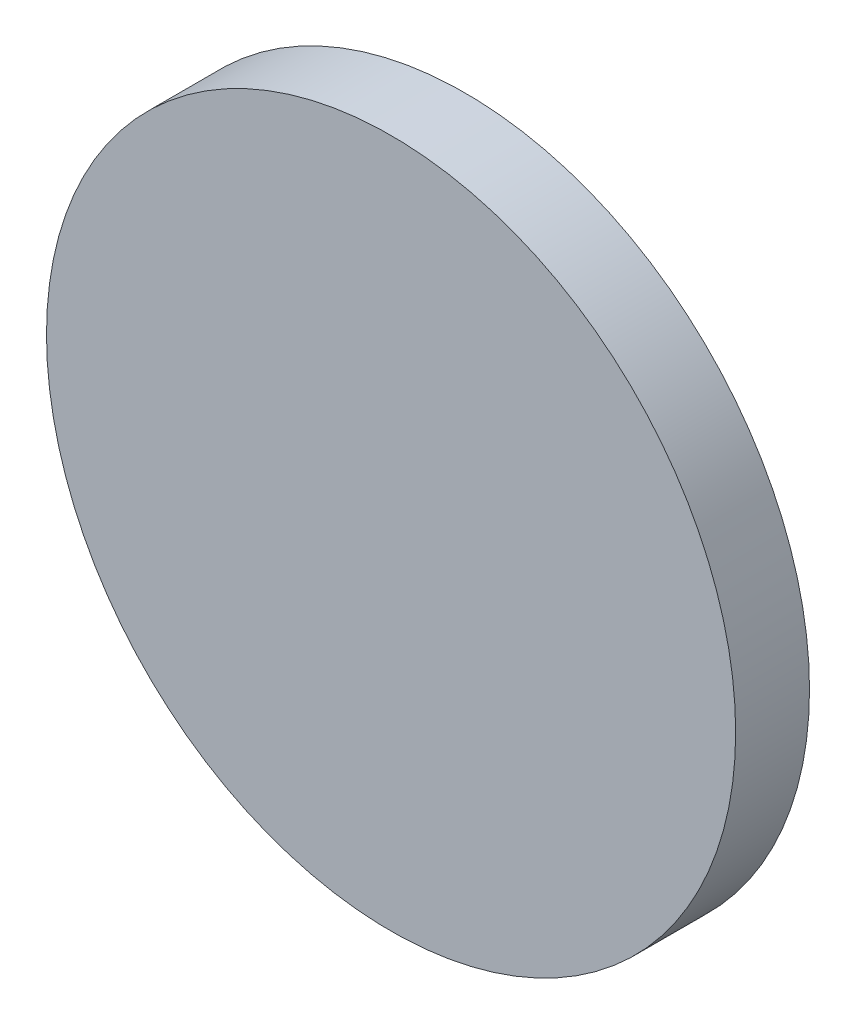
SolidWorks part; units mm, degrees
ref_plane "Front Plane" through (0, 0, 0) normal (0, 0, 1) x (1, 0, 0)
ref_plane "Top Plane" through (0, 0, 0) normal (0, 1, 0) x (1, 0, 0)
ref_plane "Right Plane" through (0, 0, 0) normal (1, 0, 0) x (0, 0, -1)
sketch "Sketch1" plane through (0, 0, 0) normal (0, 0, 1) x (1, 0, 0)
  circle A0 centre (0, 0) radius 14
  dimension "D1" = 28
extrude "Boss-Extrude1" add sketch "Sketch1" along normal blind 3
